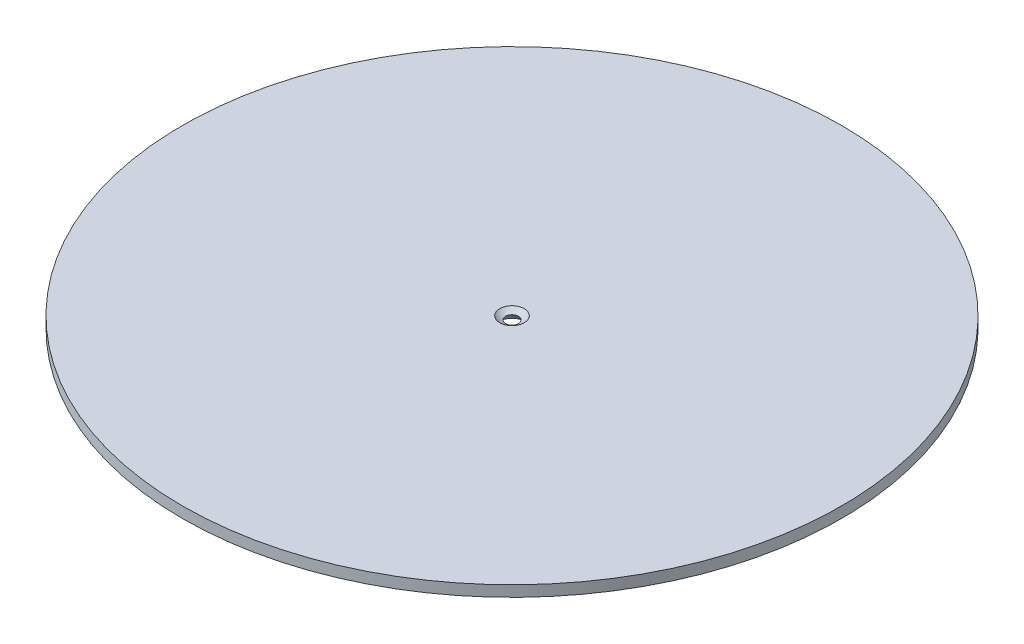
SolidWorks part; units mm, degrees
material "7075-T6 (SN)"
ref_plane "Front Plane" through (0, 0, 0) normal (0, 0, 1) x (1, 0, 0)
ref_plane "Top Plane" through (0, 0, 0) normal (0, 1, 0) x (1, 0, 0)
ref_plane "Right Plane" through (0, 0, 0) normal (1, 0, 0) x (0, 0, -1)
sketch "Sketch1" plane through (0, 0, 0) normal (0, 1, 0) x (1, 0, 0)
  circle A0 centre (0, 0) radius 1150.0002
  dimension "D1" = 2300.0005
extrude "Boss-Extrude1" add sketch "Sketch1" along normal blind 38.1
sketch "Sketch2" plane through (0, 0, 0) normal (0, 0, 1) x (1, 0, 0)
  line L0 (0, 0) -> (0, 38.1)
  line L1 (1150.0002, 38.1) -> (-1150.0002, 38.1) construction
  line L2 (0, 38.1) -> (42.7041, 38.1)
  line L3 (0, 0) -> (42.7041, 0)
  line L4 (-1150.0002, 0) -> (1150.0002, 0) construction
  arc A0 (42.7041, 0) -> (22.2813, 25.3377) centre (-15.9296, -26.3607) ccw
  arc A1 (22.2813, 25.3377) -> (42.7041, 38.1) centre (-3.2792, 88.9624) ccw
revolve "Cut-Revolve1" cut sketch "Sketch2" angle 360 about L0
